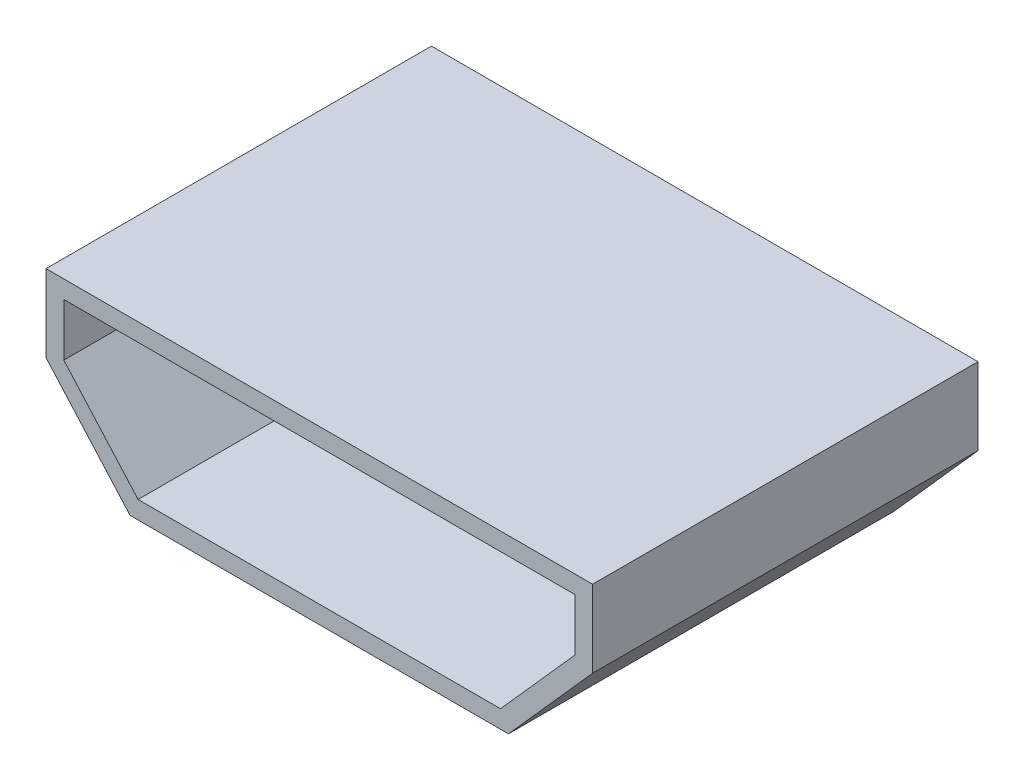
SolidWorks part; units mm, degrees
ref_plane "Front Plane" through (0, 0, 0) normal (0, 0, 1) x (1, 0, 0)
ref_plane "Top Plane" through (0, 0, 0) normal (0, 1, 0) x (1, 0, 0)
ref_plane "Right Plane" through (0, 0, 0) normal (1, 0, 0) x (0, 0, -1)
sketch "Sketch1" plane through (0, 0, 0) normal (0, 0, 1) x (1, 0, 0)
  line L0 (-2.7, 0) -> (2.7, 0)
  line L1 (2.7, 0) -> (3.9, 1.35)
  line L2 (3.9, 1.35) -> (3.9, 2.45)
  line L3 (3.9, 2.45) -> (-3.9, 2.45)
  line L4 (0, 2.45) -> (0, 0) construction
  line L5 (-3.9, 1.35) -> (-3.9, 2.45)
  line L6 (-2.7, 0) -> (-3.9, 1.35)
  dimension "D1" = 7.8
  dimension "D2" = 5.4
  dimension "D3" = 1.1
  dimension "D4" = 2.45
extrude "Boss-Extrude1" add sketch "Sketch1" along normal blind 5.5
shell "Shell1" thickness 0.254
